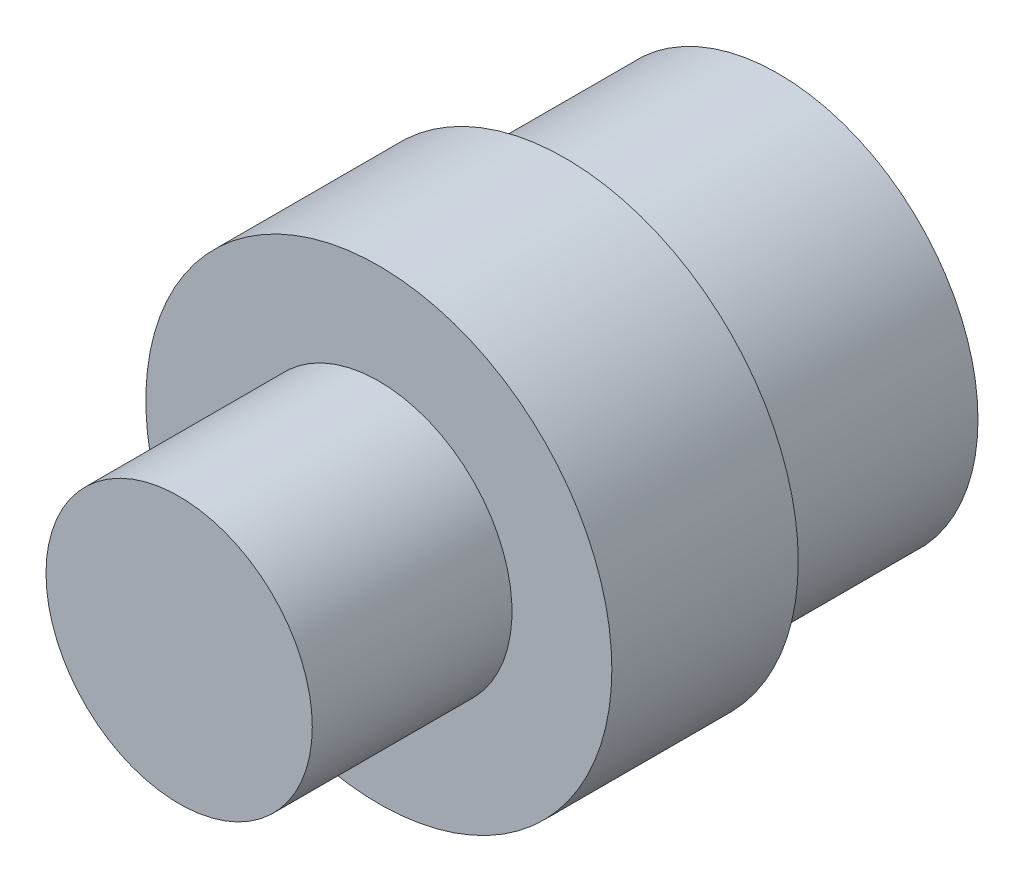
SolidWorks part; units mm, degrees
material "Plain Carbon Steel"
ref_plane "Front" through (0, 0, 0) normal (0, 0, 1) x (1, 0, 0)
ref_plane "Top" through (0, 0, 0) normal (0, 1, 0) x (1, 0, 0)
ref_plane "Right" through (0, 0, 0) normal (1, 0, 0) x (0, 0, -1)
sketch "Sketch1" plane through (0, 0, 0) normal (0, 0, 1) x (1, 0, 0)
  circle A0 centre (0, 0) radius 6.35
  dimension "D1" = 12.7
extrude "Extrude1" add sketch "Sketch1" along normal blind 9.525
sketch "Sketch2" plane through (0, 0, 0) normal (0, 0, -1) x (-1, 0, 0)
  circle A0 centre (0, 0) radius 9.525
  dimension "D1" = 19.05
extrude "Extrude2" add sketch "Sketch2" along normal blind 19.05
sketch "Sketch3" plane through (0, 0, 0) normal (0, 0, 1) x (1, 0, 0)
  circle A0 centre (0, 0) radius 11.1125
  dimension "D1" = 22.225
extrude "Extrude3" add sketch "Sketch3" against normal blind 8.89
